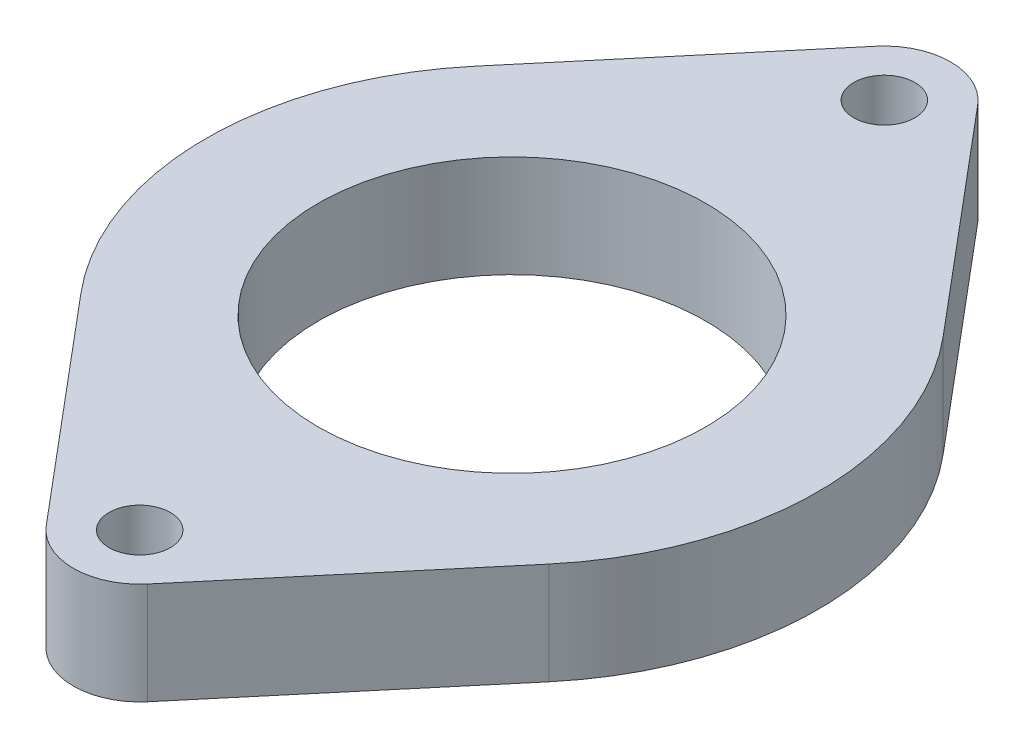
SolidWorks part; units mm, degrees
material "PEI"
ref_plane "Front Plane" through (0, 0, 0) normal (0, 0, 1) x (1, 0, 0)
ref_plane "Top Plane" through (0, 0, 0) normal (0, 1, 0) x (1, 0, 0)
ref_plane "Right Plane" through (0, 0, 0) normal (1, 0, 0) x (0, 0, -1)
sketch "Sketch1" plane through (0, 0, 0) normal (0, 1, 0) x (1, 0, 0)
  line L0 (0, -18.25) -> (0, 18.25)
  line L2 (0, 15) -> (0, -15)
  line L3 (0, 0) -> (-15, 0)
  line L5 (2.4868, 20.3425) -> (11.4775, 9.6575)
  line L6 (-2.4868, 20.3425) -> (-11.4775, 9.6575)
  line L7 (-2.4868, -20.3425) -> (-11.4775, -9.6575)
  line L8 (2.4868, -20.3425) -> (11.4775, -9.6575)
  circle A0 centre (0, 0) radius 9.5
  circle A1 centre (0, 0) radius 15
  circle A2 centre (0, 18.25) radius 1.5
  circle A3 centre (0, -18.25) radius 1.5
  circle A4 centre (0, 18.25) radius 3.25
  circle A5 centre (0, -18.25) radius 3.25
  circle A6 centre (0, -18.25) radius 1.5
  point P22 (-6.5382, 15.5276)
  point P23 (-4.6825, 17.7329)
  dimension "D1" = 19
  dimension "D2" = 30
  dimension "D5" = 3
  dimension "D3" = 30
  dimension "D4" = 18.25
extrude "Boss-Extrude1" add sketch "Sketch1" along normal blind 5
